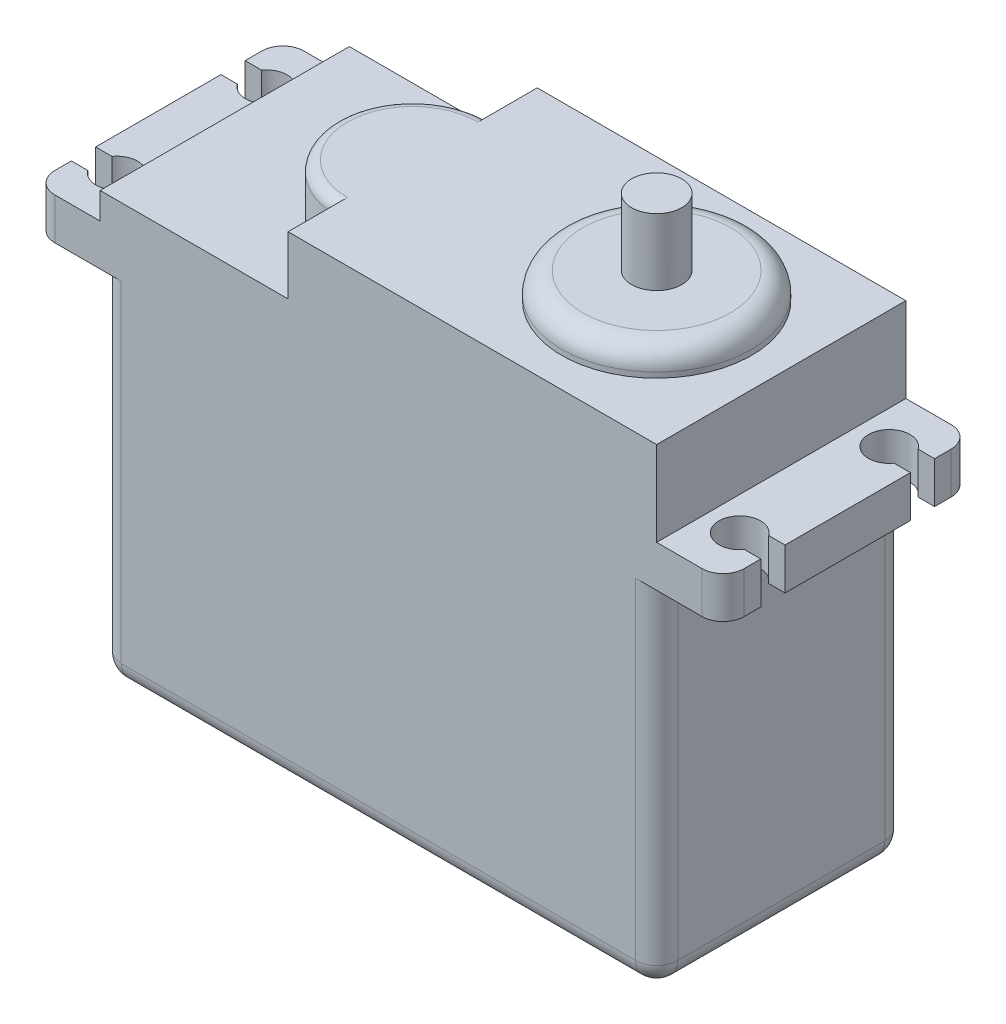
SolidWorks part; units mm, degrees
material "PE Low/Medium Density"
ref_plane "Front Plane" through (0, 0, 0) normal (0, 0, 1) x (1, 0, 0)
ref_plane "Top Plane" through (0, 0, 0) normal (0, 1, 0) x (1, 0, 0)
ref_plane "Right Plane" through (0, 0, 0) normal (1, 0, 0) x (0, 0, -1)
sketch "Sketch1" plane through (0, 0, 0) normal (0, 0, 1) x (1, 0, 0)
  line L0 (0, 25.2975) -> (0, -25.2975) construction
  line L1 (-33.5, 17.1025) -> (-41.5, 17.1025)
  line L2 (-33.5, 17.1025) -> (-33.5, -25.2975)
  line L3 (-33.5, -25.2975) -> (33.5, -25.2975)
  line L4 (33.5, 17.1025) -> (33.5, -25.2975)
  line L5 (-41.5, 17.1025) -> (-41.5, 22.1025)
  line L6 (-41.5, 22.1025) -> (-33.5, 22.1025)
  line L7 (-33.5, 22.1025) -> (-33.5, 25.2975)
  line L8 (-33.5, 25.2975) -> (-10.8777, 25.2975)
  line L9 (-10.8777, 25.2975) -> (-10.8777, 32.3025)
  line L10 (-10.8777, 32.3025) -> (33.5, 32.3025)
  line L11 (33.5, 17.1025) -> (41.5, 17.1025)
  line L12 (41.5, 17.1025) -> (41.5, 22.1025)
  line L13 (41.5, 22.1025) -> (33.5, 22.1025)
  line L14 (33.5, 22.1025) -> (33.5, 32.3025)
  dimension "D1" = 67
  dimension "D2" = 42.4
  dimension "D3" = 83
  dimension "D4" = 57.6
  dimension "D5" = 5
extrude "Extrude1" add sketch "Sketch1" along normal blind 30
fillet "Fillet1" radius 2.54 12 edges at (-33.5, -25.2975, 15) (0, -25.2975, 30) (33.5, -25.2975, 15) (0, -25.2975, 0) (41.5, 19.6025, 30) (41.5, 19.6025, 0) (33.5, -4.0975, 0) (33.5, -4.0975, 30) (-33.5, -4.0975, 30) (-33.5, -4.0975, 0) (-41.5, 19.6025, 0) (-41.5, 19.6025, 30)
sketch "Sketch2" plane through (0, 22.1025, 0) normal (0, 1, 0) x (1, 0, 0)
  line L0 (-37.5, -24) -> (-37.5, -6) construction
  line L1 (-41.5, -15) -> (41.5, -15) construction
  line L2 (-41.5, -27.46) -> (-41.5, -2.54) construction
  line L3 (41.5, -27.46) -> (41.5, -2.54) construction
  line L4 (37.5, -6) -> (37.5, -24) construction
  circle A0 centre (-37.5, -6) radius 2.5
  circle A1 centre (-37.5, -24) radius 2.5
  circle A2 centre (37.5, -6) radius 2.5
  circle A3 centre (37.5, -24) radius 2.5
  dimension "D2" = 5
  dimension "D1" = 18
  dimension "D3" = 4
  dimension "D4" = 4
extrude "Cut-Extrude1" cut sketch "Sketch2" against normal up to next
sketch "Sketch3" plane through (0, 22.1025, 0) normal (0, 1, 0) x (1, 0, 0)
  line L0 (-41.5, -15) -> (41.5, -15) construction
  line L1 (-41.5, -27.46) -> (-41.5, -2.54) construction
  line L2 (41.5, -27.46) -> (41.5, -2.54) construction
  line L3 (-40, -6) -> (40, -6) construction
  line L4 (40, -24) -> (-40, -24) construction
  line L6 (-37.551, -7.4579) -> (-41.5, -7.4579)
  line L7 (-37.551, -7.4579) -> (-37.551, -4.5421)
  line L8 (-37.551, -4.5421) -> (-41.5, -4.5421)
  line L9 (-41.5, -7.4579) -> (-41.5, -4.5421)
  line L10 (-37.551, -25.4579) -> (-41.5, -25.4579)
  line L11 (-37.551, -25.4579) -> (-37.551, -22.5421)
  line L12 (-37.551, -22.5421) -> (-41.5, -22.5421)
  line L13 (-41.5, -25.4579) -> (-41.5, -22.5421)
  line L14 (36.24, -4.5421) -> (41.5, -4.5421)
  line L15 (36.24, -4.5421) -> (36.24, -7.4579)
  line L16 (36.24, -7.4579) -> (41.5, -7.4579)
  line L17 (41.5, -4.5421) -> (41.5, -7.4579)
  line L18 (36.9891, -22.5421) -> (41.5, -22.5421)
  line L19 (36.9891, -22.5421) -> (36.9891, -25.4579)
  line L20 (36.9891, -25.4579) -> (41.5, -25.4579)
  line L21 (41.5, -22.5421) -> (41.5, -25.4579)
  circle A0 centre (-37.5, -6) radius 2.5 construction
  circle A1 centre (37.5, -6) radius 2.5 construction
  circle A2 centre (37.5, -24) radius 2.5 construction
  circle A3 centre (-37.5, -24) radius 2.5 construction
extrude "Cut-Extrude2" cut sketch "Sketch3" against normal up to next
sketch "Sketch4" plane through (0, 25.2975, 0) normal (0, 1, 0) x (1, 0, 0)
  line L0 (-10.8777, -30) -> (-10.8777, 0) construction
  line L1 (-10.8777, -5.8698) -> (-10.8777, -24.1302)
  arc A0 (-10.8777, -5.8698) -> (-10.8777, -24.1302) centre (-10.8777, -15) ccw
extrude "Extrude2" add sketch "Sketch4" along normal up to surface (7.0049 mm away) up to face at (11.3112, 32.3025, 15)
sketch "Sketch5" plane through (0, 32.3025, 0) normal (0, 1, 0) x (1, 0, 0)
  line L0 (33.5, -15) -> (-41.5, -15) construction
  line L1 (33.5, -30) -> (33.5, 0) construction
  line L2 (-41.5, -22.5421) -> (-41.5, -7.4579) construction
  circle A0 centre (18.5, -15) radius 11.43
  dimension "D1" = 22.86
  dimension "D2" = 15
extrude "Extrude3" add sketch "Sketch5" along normal blind 3.175
fillet "Fillet2" radius 2.54 1 edges at (18.5, 35.4775, 26.43)
fillet "Fillet3" radius 1.27 1 edges at (-20.0079, 32.3025, 15)
sketch "Sketch6" plane through (0, 35.4775, 0) normal (0, 1, 0) x (1, 0, 0)
  circle A0 centre (18.5, -15) radius 3.013
extrude "Extrude4" add sketch "Sketch6" along normal offset from surface (8.025 mm away) 68.8 up to face at (0, -25.2975, 15)
